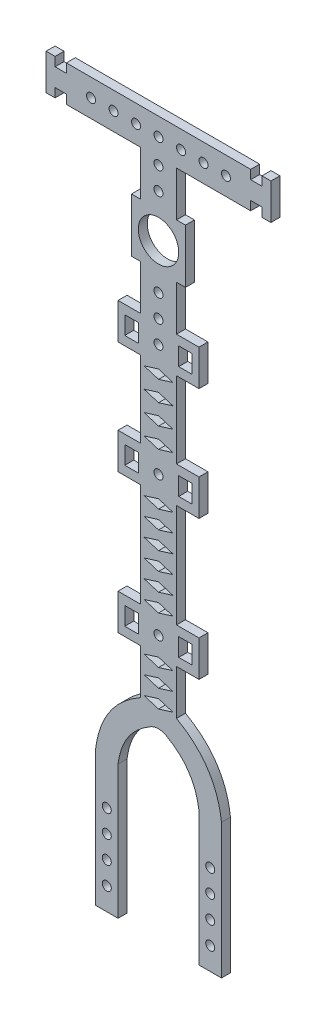
SolidWorks part; units mm, degrees
ref_plane "前视基准面" through (0, 0, 0) normal (0, 0, 1) x (1, 0, 0)
ref_plane "上视基准面" through (0, 0, 0) normal (0, 1, 0) x (1, 0, 0)
ref_plane "右视基准面" through (0, 0, 0) normal (1, 0, 0) x (0, 0, -1)
other "Configuration Table"
sketch "草图1" plane through (0, 0, 0) normal (0, 0, 1) x (1, 0, 0)
  line L0 (0, 0) -> (0, -7.7648) construction
  line L1 (0, 0) -> (8.7713, 0) construction
  line L2 (-4, 6) -> (-4, 16)
  line L3 (-6, 6) -> (6, 6)
  line L4 (-6, 6) -> (-6, -6)
  line L5 (-6, -6) -> (6, -6)
  line L6 (6, 6) -> (6, -6)
  line L7 (-6, 6) -> (6, -6) construction
  line L8 (-6, -6) -> (6, 6) construction
  line L9 (-4, 16) -> (-20.5, 16)
  line L10 (-25, 16) -> (-25, 24)
  line L11 (-25, 24) -> (-23, 24)
  line L12 (25, 24) -> (25, 16)
  line L13 (25, 16) -> (23, 16)
  line L14 (4, 16) -> (4, 6)
  line L15 (-23, 24) -> (-23, 22)
  line L16 (-23, 22) -> (-20.5, 22)
  line L17 (-20.5, 22) -> (-20.5, 24)
  line L18 (-23, 16) -> (-23, 18)
  line L19 (-23, 18) -> (-20.5, 18)
  line L20 (-20.5, 18) -> (-20.5, 16)
  line L21 (20.5, 24) -> (20.5, 22)
  line L22 (20.5, 22) -> (23, 22)
  line L23 (23, 22) -> (23, 24)
  line L24 (23, 16) -> (23, 18)
  line L25 (23, 18) -> (20.5, 18)
  line L26 (20.5, 18) -> (20.5, 16)
  line L27 (-20.5, 24) -> (20.5, 24)
  line L28 (-23, 16) -> (-25, 16)
  line L29 (23, 24) -> (25, 24)
  line L30 (20.5, 16) -> (4, 16)
  line L31 (-25, 20) -> (-15.0369, 20) construction
  line L32 (0, 20) -> (5, 20) construction
  line L33 (0, 20) -> (-5, 20) construction
  line L34 (-4, -6) -> (-4, -16)
  line L35 (-4, -16) -> (-9, -16)
  line L36 (-9, -16) -> (-9, -24)
  line L37 (-9, -24) -> (-4, -24)
  line L38 (-4, -24) -> (-4, -41)
  line L39 (-4, -41) -> (-9, -41)
  line L40 (-9, -41) -> (-9, -49)
  line L41 (-9, -49) -> (-4, -49)
  line L42 (-4, -49) -> (-4, -72)
  line L43 (-4, -72) -> (-9, -72)
  line L44 (-9, -72) -> (-9, -80)
  line L45 (-9, -80) -> (-4, -80)
  line L46 (-4, -80) -> (-4, -90)
  line L47 (-14, -135) -> (-9, -135)
  line L48 (4, -90) -> (4, -80)
  line L49 (4, -80) -> (9, -80)
  line L50 (9, -80) -> (9, -72)
  line L51 (9, -72) -> (4, -72)
  line L52 (4, -72) -> (4, -49)
  line L53 (4, -49) -> (9, -49)
  line L54 (9, -49) -> (9, -41)
  line L55 (9, -41) -> (4, -41)
  line L56 (4, -41) -> (4, -24)
  line L57 (4, -24) -> (9, -24)
  line L58 (9, -24) -> (9, -16)
  line L59 (9, -16) -> (4, -16)
  line L60 (4, -16) -> (4, -6)
  line L61 (-8.8729, -20) -> (-3.8729, -20) construction
  line L62 (7.5, -22) -> (4.5, -22)
  line L63 (-7.5, -18) -> (-4.5, -18)
  line L64 (-7.5, -18) -> (-7.5, -22)
  line L65 (-7.5, -22) -> (-4.5, -22)
  line L66 (-4.5, -18) -> (-4.5, -22)
  line L67 (-7.5, -18) -> (-4.5, -22) construction
  line L68 (-7.5, -22) -> (-4.5, -18) construction
  line L69 (4.5, -18) -> (4.5, -22)
  line L70 (7.5, -18) -> (4.5, -18)
  line L71 (7.5, -18) -> (7.5, -22)
  line L72 (-4, -32.5) -> (4, -32.5) construction
  line L73 (7.5, -47) -> (7.5, -43)
  line L74 (7.5, -47) -> (4.5, -47)
  line L75 (4.5, -47) -> (4.5, -43)
  line L76 (7.5, -43) -> (4.5, -43)
  line L77 (-7.5, -43) -> (-4.5, -43)
  line L78 (-4.5, -47) -> (-4.5, -43)
  line L79 (-7.5, -47) -> (-4.5, -47)
  line L80 (-7.5, -47) -> (-7.5, -43)
  line L81 (-4, -60.5) -> (4, -60.5) construction
  line L82 (7.5, -74) -> (4.5, -74)
  line L83 (4.5, -74) -> (4.5, -78)
  line L84 (7.5, -78) -> (4.5, -78)
  line L85 (7.5, -74) -> (7.5, -78)
  line L86 (-7.5, -74) -> (-7.5, -78)
  line L87 (-7.5, -74) -> (-4.5, -74)
  line L88 (-4.5, -74) -> (-4.5, -78)
  line L89 (-7.5, -78) -> (-4.5, -78)
  line L90 (-14, -105) -> (-14, -135)
  line L93 (14, -105) -> (14, -135)
  line L94 (-9, -105.3077) -> (-9, -135)
  line L95 (9, -135) -> (14, -135)
  line L96 (-9, -45) -> (9, -45) construction
  line L97 (9, -105.3077) -> (9, -135)
  line L103 (0, -33.7) -> (-3.2, -34.7)
  line L104 (-3.2, -34.7) -> (0, -35.7)
  line L117 (0, -53.7) -> (-3.2, -54.7)
  line L118 (-3.2, -54.7) -> (0, -55.7)
  line L140 (-11.5, -135) -> (-11.5, -106.6492) construction
  line L141 (0, -49.7) -> (-3.2, -50.7)
  line L142 (-3.2, -50.7) -> (0, -51.7)
  line L143 (0, -51.7) -> (3.2, -50.7)
  line L144 (3.2, -50.7) -> (0, -49.7)
  line L145 (0, -55.7) -> (3.2, -54.7)
  line L146 (3.2, -54.7) -> (0, -53.7)
  line L147 (0, -57.7) -> (-3.2, -58.7)
  line L148 (-3.2, -58.7) -> (0, -59.7)
  line L149 (0, -59.7) -> (3.2, -58.7)
  line L150 (3.2, -58.7) -> (0, -57.7)
  line L151 (0, -61.7) -> (-3.2, -62.7)
  line L152 (-3.2, -62.7) -> (0, -63.7)
  line L153 (0, -63.7) -> (3.2, -62.7)
  line L154 (3.2, -62.7) -> (0, -61.7)
  line L155 (0, -65.7) -> (-3.2, -66.7)
  line L156 (-3.2, -66.7) -> (0, -67.7)
  line L157 (0, -67.7) -> (3.2, -66.7)
  line L158 (3.2, -66.7) -> (0, -65.7)
  line L159 (0, -69.7) -> (-3.2, -70.7)
  line L160 (-3.2, -70.7) -> (0, -71.7)
  line L161 (0, -71.7) -> (3.2, -70.7)
  line L162 (3.2, -70.7) -> (0, -69.7)
  line L183 (0, -73.7) -> (-3.2, -74.7) [skipped]
  line L184 (-3.2, -74.7) -> (0, -75.7) [skipped]
  line L185 (0, -75.7) -> (3.2, -74.7) [skipped]
  line L186 (3.2, -74.7) -> (0, -73.7) [skipped]
  line L187 (0, -77.7) -> (-3.2, -78.7) [skipped]
  line L188 (-3.2, -78.7) -> (0, -79.7) [skipped]
  line L189 (0, -79.7) -> (3.2, -78.7) [skipped]
  line L190 (3.2, -78.7) -> (0, -77.7) [skipped]
  line L191 (0, -81.7) -> (-3.2, -82.7) [skipped]
  line L192 (3.2, -82.7) -> (0, -81.7) [skipped]
  line L193 (0, -83.7) -> (3.2, -82.7) [skipped]
  line L194 (-3.2, -82.7) -> (0, -83.7) [skipped]
  line L195 (0, -85.7) -> (-3.2, -86.7) [skipped]
  line L196 (-3.2, -86.7) -> (0, -87.7) [skipped]
  line L197 (0, -87.7) -> (3.2, -86.7) [skipped]
  line L198 (3.2, -86.7) -> (0, -85.7) [skipped]
  line L199 (0, -89.7) -> (-3.2, -90.7) [skipped]
  line L200 (-3.2, -90.7) -> (0, -91.7) [skipped]
  line L201 (0, -91.7) -> (3.2, -90.7) [skipped]
  line L202 (3.2, -90.7) -> (0, -89.7) [skipped]
  line L206 (0, -80.2) -> (-3.2, -81.2)
  line L207 (-3.2, -81.2) -> (0, -82.2)
  line L208 (0, -82.2) -> (3.2, -81.2)
  line L209 (3.2, -81.2) -> (0, -80.2)
  line L210 (0, -84.2) -> (-3.2, -85.2)
  line L211 (-3.2, -85.2) -> (0, -86.2)
  line L212 (0, -86.2) -> (3.2, -85.2)
  line L213 (3.2, -85.2) -> (0, -84.2)
  line L214 (0, -88.2) -> (-3.2, -89.2)
  line L215 (-3.2, -89.2) -> (0, -90.2)
  line L216 (0, -90.2) -> (3.2, -89.2)
  line L217 (3.2, -89.2) -> (0, -88.2)
  line L218 (0, -38.2) -> (-3.2, -39.2)
  line L219 (-3.2, -39.2) -> (0, -40.2)
  line L220 (0, -40.2) -> (3.2, -39.2)
  line L221 (3.2, -39.2) -> (0, -38.2)
  line L222 (0, -35.7) -> (3.2, -34.7)
  line L223 (3.2, -34.7) -> (0, -33.7)
  line L224 (0, -29.2) -> (-3.2, -30.2)
  line L225 (-3.2, -30.2) -> (0, -31.2)
  line L226 (0, -31.2) -> (3.2, -30.2)
  line L227 (3.2, -30.2) -> (0, -29.2)
  line L228 (0, -24.7) -> (-3.2, -25.7)
  line L229 (-3.2, -25.7) -> (0, -26.7)
  line L230 (0, -26.7) -> (3.2, -25.7)
  line L231 (3.2, -25.7) -> (0, -24.7)
  line L232 (-9, -76) -> (9, -76) construction
  circle A0 centre (0, 0) radius 4.5
  circle A1 centre (0, 9.5405) radius 1
  circle A2 centre (0, 14.5405) radius 1
  circle A3 centre (0, 20) radius 1
  circle A4 centre (5, 20) radius 1
  circle A5 centre (10, 20) radius 1
  circle A6 centre (15, 20) radius 1
  circle A7 centre (-5, 20) radius 1
  circle A8 centre (-10, 20) radius 1
  circle A9 centre (-15, 20) radius 1
  circle A10 centre (0, -20) radius 1
  circle A11 centre (0, -15) radius 1
  circle A12 centre (0, -10) radius 1
  circle A13 centre (0, -45) radius 1
  circle A14 centre (-11.5, -130) radius 1
  circle A15 centre (-11.5, -125) radius 1
  circle A16 centre (-11.5, -120) radius 1
  circle A17 centre (-11.5, -115) radius 1
  circle A18 centre (11.5, -130) radius 1
  circle A19 centre (11.5, -125) radius 1
  circle A20 centre (11.5, -120) radius 1
  circle A21 centre (11.5, -115) radius 1
  circle A22 centre (0, -76) radius 1
  spline S0 degree 2 poles (-4, -90) (-12.8248, -94.9465) (-14, -105) knots 0 0 0 1 1 1
  spline S1 degree 2 poles (4, -90) (12.8248, -94.9465) (14, -105) knots 0 0 0 1 1 1
  spline S2 degree 1 poles (-1.5553, -94.3616) (-9, -105.3077) knots 0 0 1 1 construction
  spline S3 degree 2 poles (-1.5553, -94.3616) (-4.1241, -95.8241) (-6.7724, -98.8517) (-8.6016, -102.4141) (-9, -105.3077) knots 0 0 0 0.368595 0.614325 0.98292 0.98292 0.98292
  spline S4 degree 2 poles (-1.5553, -94.3616) (0, -93.6523) (1.5553, -94.3616) knots 0 0 0 1 1 1
  spline S8 degree 1 poles (1.5553, -94.3616) (9, -105.3077) knots 0 0 1 1 construction
  spline S9 degree 2 poles (1.5553, -94.3616) (4.1241, -95.8241) (6.7724, -98.8517) (8.6016, -102.4141) (9, -105.3077) knots 0 0 0 0.368595 0.614325 0.98292 0.98292 0.98292
  point P88 (-6, -20)
  point P90 (-6, -20)
  point P119 (-14, -105)
  point P144 (0, -34.7)
  point P148 (0, -50.7)
  point P150 (0, -30.2)
  point P155 (0, -25.7)
  point P157 (0, -78.7)
  point P158 (0, -54.7)
  point P163 (0, -58.7)
  point P168 (0, -62.7)
  point P174 (0, -86.7)
  point P175 (0, -82.7)
  point P176 (0, -39.2)
  point P182 (0, -81.2)
  point P204 (0, -66.7)
  point P209 (0, -70.7)
  point P214 (0, -90.7)
  point P215 (0, -74.7)
  point P220 (0, -85.2)
  point P225 (0, -89.2)
  dimension "D1" = 9
  dimension "D17" = 2
  dimension "D19" = 2
  dimension "D43" = 2
  dimension "D45" = 2
  dimension "D58" = 2
  dimension "D47" = 2
  dimension "D2" = 12
  dimension "D3" = 12
  dimension "D4" = 2
  dimension "D5" = 2
  dimension "D6" = 10
  dimension "D7" = 8
  dimension "D8" = 21
  dimension "D9" = 50
  dimension "D10" = 21
  dimension "D11" = 2
  dimension "D12" = 2.5
  dimension "D13" = 2
  dimension "D14" = 2
  dimension "D15" = 2.5
  dimension "D16" = 2
  dimension "D21" = 5
  dimension "D23" = 5
  dimension "D24" = 2
  dimension "D25" = 2
  dimension "D26" = 10
  dimension "D27" = 5
  dimension "D28" = 8
  dimension "D29" = 8
  dimension "D30" = 4
  dimension "D31" = 3
  dimension "D32" = 4
  dimension "D33" = 4
  dimension "D34" = 1.5
  dimension "D35" = 17
  dimension "D36" = 23
  dimension "D37" = 10
  dimension "D38" = 10
  dimension "D39" = 15
  dimension "D40" = 45
  dimension "D46" = 4
  dimension "D51" = 6.4
  dimension "D53" = 2
  dimension "D54" = 11
  dimension "D59" = 5
  dimension "D41" = 5
  dimension "D42" = 5
  dimension "D18" = 2
  dimension "D20" = 4
  dimension "D22" = 4
  dimension "D44" = 3
  dimension "D60" = 4
extrude "凸台-拉伸1" add sketch "草图1" along normal blind 2 contours L30 L26 L25 L24 L13 L12 L29 L23 L22 L21 L27 L17 L16 L15 L11 L10 L28 L18 L19 L20 L9 L2 L3 L14 A9 A8 A7 A6 A5 A4 A3 A2 A1 | L6 L3 L4 L5 A0 | S4 S9 L97 L95 L93 S1 L48 L49 L50 L51 L52 L53 L54 L55 L56 L57 L58 L59 L60 L5 L34 L35 L36 L37 L38 L39 L40 L41 L42 L43 L44 L45 L46 S0 L90 L47 L94 S3 A21 A19 L82 L85 L84 L83 L79 L80 L77
